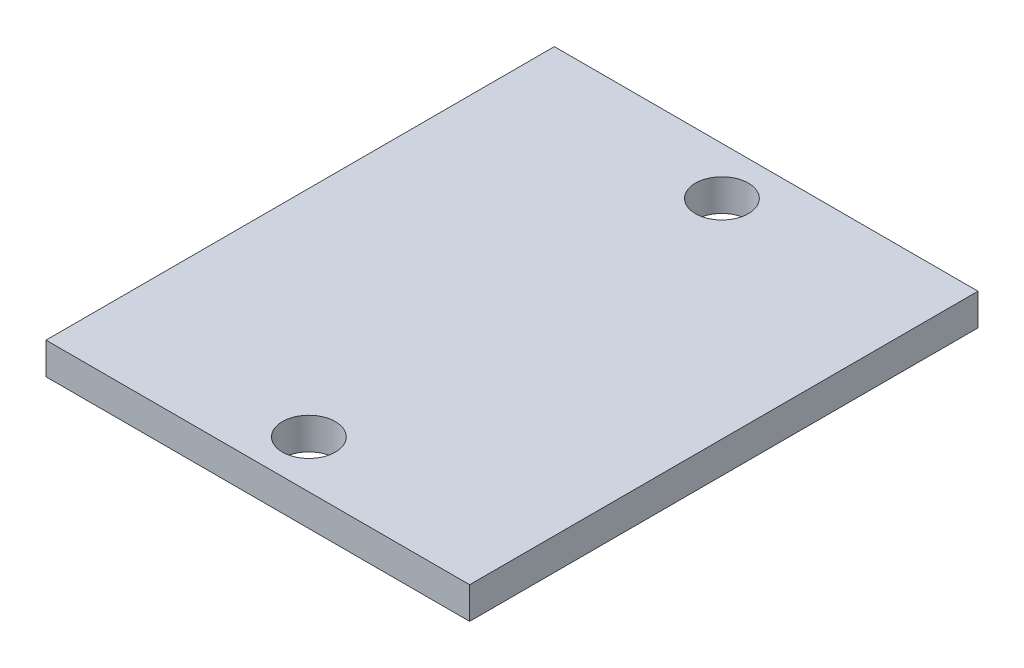
SolidWorks part; units mm, degrees
ref_plane "Front Plane" through (0, 0, 0) normal (0, 0, 1) x (1, 0, 0)
ref_plane "Top Plane" through (0, 0, 0) normal (0, 1, 0) x (1, 0, 0)
ref_plane "Right Plane" through (0, 0, 0) normal (1, 0, 0) x (0, 0, -1)
sketch "Sketch2" plane through (0, 0, 0) normal (0, 1, 0) x (1, 0, 0)
  line L0 (20, -12) -> (0, -12) construction
  line L1 (0, 0) -> (20, 0)
  line L2 (0, 0) -> (0, -24)
  line L3 (0, -24) -> (20, -24)
  line L4 (20, 0) -> (20, -24)
  circle A6 centre (10.16, -2.25) radius 1.25
  circle A8 centre (10.16, -21.75) radius 1.25
  dimension "D3" = 2.5
  dimension "D6" = 9.84
  dimension "D7" = 2.25
  dimension "D1" = 20
  dimension "D2" = 24
  dimension "D8" = 2.25
extrude "Boss-Extrude1" add sketch "Sketch2" along normal blind 1.5
